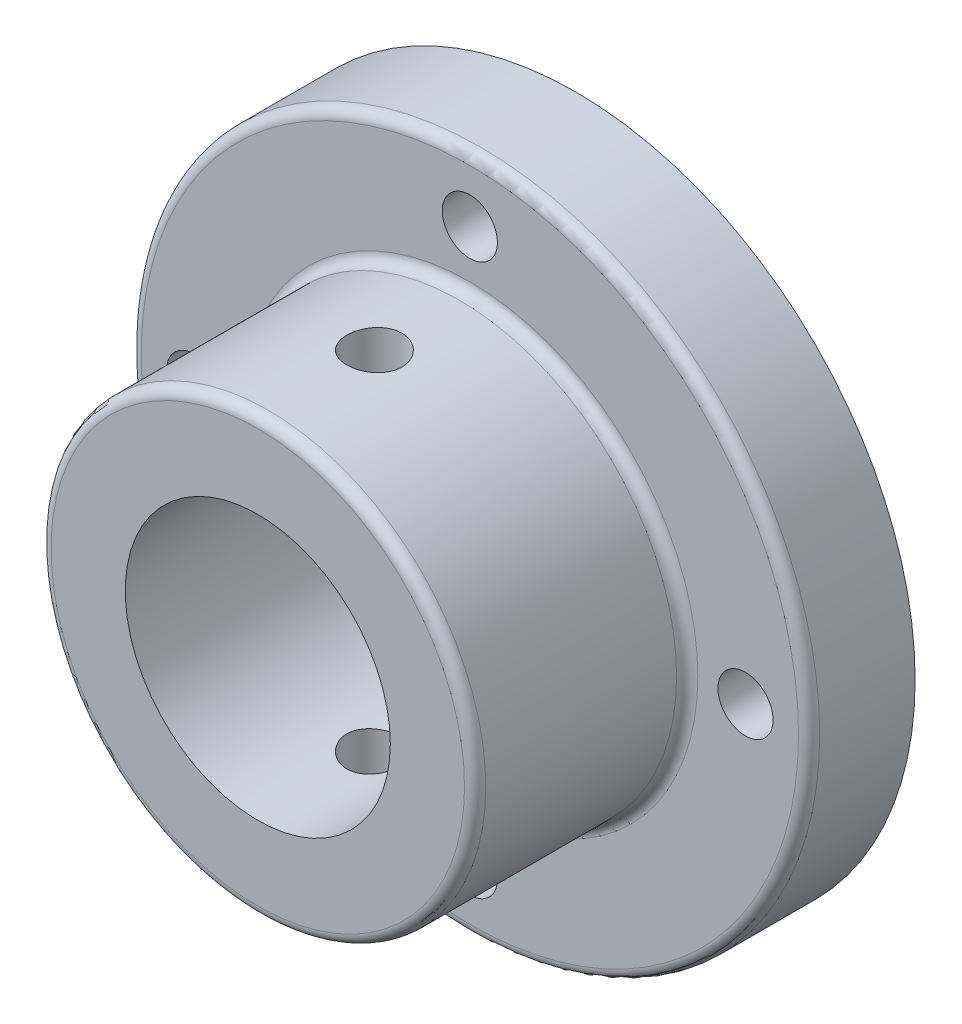
SolidWorks part; units mm, degrees
material "PVC 0.007 Plasticized"
ref_plane "Front Plane" through (0, 0, 0) normal (0, 0, 1) x (1, 0, 0)
ref_plane "Top Plane" through (0, 0, 0) normal (0, 1, 0) x (1, 0, 0)
ref_plane "Right Plane" through (0, 0, 0) normal (1, 0, 0) x (0, 0, -1)
sketch "Sketch1" plane through (0, 0, 0) normal (0, 0, 1) x (1, 0, 0)
  circle A0 centre (0, 0) radius 16
  circle A1 centre (0, 0) radius 13 construction
  circle A2 centre (0, 13) radius 1.3
  circle A3 centre (13, 0) radius 1.3
  circle A4 centre (0, -13) radius 1.3
  circle A5 centre (-13, 0) radius 1.3
  circle A6 centre (0, 0) radius 6.25
  point P15 (0, 0)
  dimension "D1" = 32
  dimension "D2" = 26
  dimension "D3" = 2.6
  dimension "D5" = 12.5
  dimension "D4" = 4
extrude "Boss-Extrude1" add sketch "Sketch1" along normal blind 5
sketch "Sketch3" plane through (0, 0, 0) normal (0, 0, 1) x (1, 0, 0)
  circle A0 centre (0, 0) radius 6.25
  circle A1 centre (0, 0) radius 10.25
  dimension "D1" = 12.5
  dimension "D2" = 4
extrude "Boss-Extrude2" add sketch "Sketch3" along normal blind 15
sketch "Sketch4" plane through (0, 0, 0) normal (0, 1, 0) x (1, 0, 0)
  line L0 (0, -15) -> (0, -5) construction
  line L1 (-10.25, -15) -> (10.25, -15) construction
  circle A0 centre (0, -9.5) radius 1.3
  dimension "D1" = 2.6
  dimension "D2" = 5.5
extrude "Cut-Extrude5" cut sketch "Sketch4" against normal through all both and the other way through all
fillet "Fillet1" radius 0.5 3 edges at (10.25, 0, 5) (16, 0, 5) (10.25, 0, 15)
